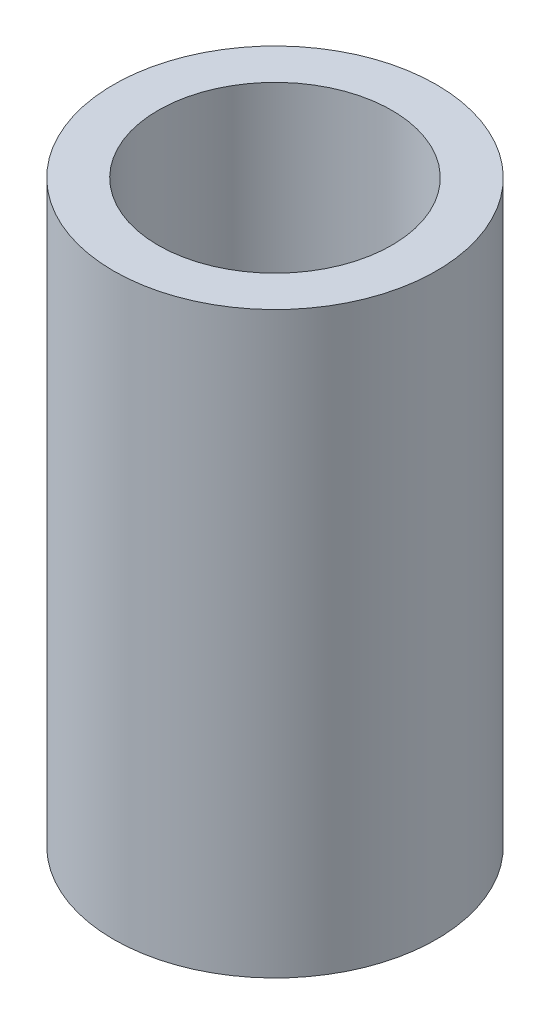
SolidWorks part; units mm, degrees
ref_plane "Alzado" through (0, 0, 0) normal (0, 0, 1) x (1, 0, 0)
ref_plane "Planta" through (0, 0, 0) normal (0, 1, 0) x (1, 0, 0)
ref_plane "Vista lateral" through (0, 0, 0) normal (1, 0, 0) x (0, 0, -1)
sketch "Croquis1" plane through (0, 0, 0) normal (0, 1, 0) x (1, 0, 0)
  circle A0 centre (0, 0) radius 7.25
  circle A1 centre (0, 0) radius 5.25
  dimension "D1" = 10.5
  dimension "D2" = 2
extrude "Saliente-Extruir1" add sketch "Croquis1" along normal blind 26
